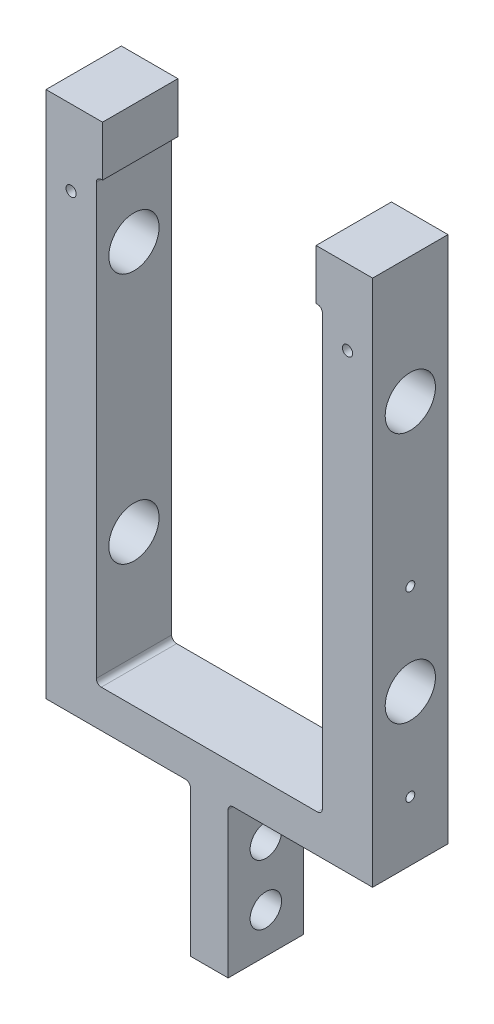
SolidWorks part; units mm, degrees
material "6061 Alloy"
ref_plane "Front Plane" through (0, 0, 0) normal (0, 0, 1) x (1, 0, 0)
ref_plane "Top Plane" through (0, 0, 0) normal (0, 1, 0) x (1, 0, 0)
ref_plane "Right Plane" through (0, 0, 0) normal (1, 0, 0) x (0, 0, -1)
sketch "Sketch1" plane through (0, 0, 0) normal (0, 0, 1) x (1, 0, 0)
  line L7 (9.525, 0) -> (-9.525, 0)
  line L13 (-9.525, 0) -> (-9.525, 19.05)
  line L14 (-9.525, 19.05) -> (-41.275, 19.05)
  line L15 (-41.275, 19.05) -> (-41.275, 131.5967)
  line L17 (-28.575, 139.7) -> (-28.575, 28.575)
  line L18 (-28.575, 28.575) -> (28.575, 28.575)
  line L19 (0, 29.8154) -> (0, -13.1535) construction
  line L20 (28.575, 139.7) -> (28.575, 28.575)
  line L22 (41.275, 19.05) -> (41.275, 131.5967)
  line L23 (9.525, 19.05) -> (41.275, 19.05)
  line L24 (9.525, 0) -> (9.525, 19.05)
  line L25 (41.275, 131.5967) -> (41.275, 152.4)
  line L26 (41.275, 152.4) -> (-41.275, 152.4)
  line L27 (-41.275, 152.4) -> (-41.275, 131.5967)
  line L29 (28.575, 139.7) -> (-28.575, 139.7)
  point P12 (0, 28.575)
  point P17 (0, 0)
  dimension "D1" = 19.05
  dimension "D2" = 57.15
  dimension "D3" = 19.05
  dimension "D4" = 82.55
  dimension "D5" = 111.125
  dimension "D6" = 12.7
  dimension "D7" = 152.4
extrude "Boss-Extrude1" add sketch "Sketch1" along normal mid plane 19.05
sketch "Sketch2" plane through (-41.275, 0, 0) normal (-1, 0, 0) x (0, 0, 1)
  line L0 (-26.0251, 0) -> (40.3307, 0) construction
  line L1 (0, 127) -> (0, 0) construction
  circle A0 centre (0, 57.15) radius 6.35
  circle A1 centre (0, 120.65) radius 6.35
  dimension "D2" = 12.7
  dimension "D1" = 12.7
  dimension "D4" = 63.5
  dimension "D3" = 57.15
extrude "Cut-Extrude1" cut sketch "Sketch2" against normal through all
sketch "Sketch4" plane through (0, 0, -9.525) normal (0, 0, -1) x (-1, 0, 0)
  line L1 (9.525, 0) -> (-9.525, 0) construction
  line L2 (9.525, 0) -> (9.525, 19.05) construction
  line L3 (9.525, 19.05) -> (-9.525, 19.05) construction
  line L4 (-9.525, 0) -> (-9.525, 19.05) construction
  line L5 (-4.7625, 19.0579) -> (4.7625, 19.0579) construction
  line L6 (-4.7625, 19.0579) -> (-4.7625, 0) construction
  line L7 (-4.7625, 0) -> (4.7625, 0) construction
  line L8 (4.7625, 19.0579) -> (4.7625, 0) construction
  line L9 (-4.7625, 19.0579) -> (4.7625, 0) construction
  line L10 (-4.7625, 0) -> (4.7625, 19.0579) construction
  line L11 (-9.525, 19.05) -> (-4.7625, 19.05)
  line L12 (-9.525, 19.05) -> (-9.525, 0)
  line L13 (-9.525, 0) -> (-4.7625, 0)
  line L14 (-4.7625, 19.05) -> (-4.7625, 0)
  line L15 (4.7625, 19.0579) -> (9.525, 19.0579)
  line L16 (4.7625, 19.0579) -> (4.7625, 0)
  line L17 (4.7625, 0) -> (9.525, 0)
  line L18 (9.525, 19.0579) -> (9.525, 0)
  point P6 (0, 9.529)
  dimension "D1" = 9.525
extrude "Cut-Extrude2" cut sketch "Sketch4" against normal through all
sketch "Sketch5" plane through (-4.7625, 0, 0) normal (-1, 0, 0) x (0, 0, 1)
  circle A0 centre (0, 6.35) radius 4.7625
  dimension "D1" = 9.525
  dimension "D2" = 6.35
sketch "Sketch6" plane through (41.275, 0, 0) normal (-1, 0, 0) x (0, 0, 1)
  line L0 (0, 80.1624) -> (0, 34.1376) construction
  point P5 (0, 57.15)
  dimension "D1" = 46.0248
hole_wizard "#4-40 Tapped Hole2" positions "Sketch12" profile "Sketch13" tap size "#4-40" standard "ANSI Inch"
sketch "Sketch12" plane through (41.275, 0, 0) normal (1, 0, 0) x (0, 0, -1)
  point P0 (0, 80.1624)
  point P3 (0, 34.1376)
sketch "Sketch13" plane through (41.275, 80.1624, 0) normal (0, 1, 0) x (0, 0, -1)
  line L0 (0, 0) -> (0, 13.3792)
  line L1 (0, 13.3792) -> (1.1303, 12.7)
  line L2 (1.1303, 12.7) -> (1.1303, 0)
  line L5 (1.1303, 0) -> (0, 0)
  line L10 (0, 13.3792) -> (-1.1303, 12.7) construction
  line L11 (0, -6.35) -> (0, 107.95) construction
  dimension "Tap Drill Dia." = 2.2606
  dimension "Tap Drill Depth" = 12.7
  dimension "Drill Angle" = 118
cosmetic thread "Hole Thread5" parameters "D1"=82.55, "D2"=2.8448
cosmetic thread "Hole Thread6" parameters "D1"=82.55, "D2"=2.8448
sketch "Sketch14" plane through (0, 0, 0) normal (0, -1, 0) x (1, 0, 0)
  line L1 (4.7625, -9.525) -> (-4.7625, -9.525)
  line L2 (4.7625, -9.525) -> (4.7625, 9.525)
  line L3 (4.7625, 9.525) -> (-4.7625, 9.525)
  line L4 (-4.7625, -9.525) -> (-4.7625, 9.525)
extrude "Boss-Extrude2" add sketch "Sketch14" along normal blind 19.05
hole_wizard "Hole1" positions "Sketch15" profile "Sketch16" legacy end condition through all
sketch "Sketch15" plane through (-4.7625, 0, 0) normal (-1, 0, 0) x (0, 0, 1)
  point P0 (0, 6.35)
  point P3 (0, -8.89)
  dimension "D1" = 8.89
sketch "Sketch16" plane through (-4.7625, 6.35, 0) normal (0, 1, 0) x (0, 0, 1)
  line L0 (0, 0) -> (0, 48.4245)
  line L1 (0, 48.4245) -> (3.9726, 46.0375)
  line L2 (3.9726, 46.0375) -> (3.9726, 0)
  line L4 (3.9726, 0) -> (0, 0)
  line L6 (0, 48.4245) -> (-3.9726, 46.0375) construction
  line L7 (0, -4.2442) -> (0, 117.3081) construction
  dimension "Diameter" = 7.9451
  dimension "Depth" = 46.0375
  dimension "Drill Angle" = 118
fillet "Fillet1" radius 1.27 6 edges at (4.7625, 19.05, 0) (-4.7625, 19.0579, 0) (-28.575, 28.575, 0) (28.575, 28.575, 0) (28.575, 139.7, 0) (-28.575, 139.7, 0)
sketch "Sketch17" plane through (0, 0, 9.525) normal (0, 0, 1) x (1, 0, 0)
  line L0 (0, 152.4) -> (0, 117.2896) construction
  line L1 (41.275, 152.4) -> (-41.275, 152.4) construction
  line L2 (23.5336, 152.4) -> (23.5336, 139.7) construction
  line L3 (27.305, 139.7) -> (-27.305, 139.7) construction
  line L4 (23.5336, 146.05) -> (-38.274, 146.05) construction
  line L6 (-26.9875, 152.4) -> (26.9875, 152.4)
  line L7 (-26.9875, 152.4) -> (-26.9875, 139.7)
  line L8 (-26.9875, 139.7) -> (26.9875, 139.7)
  line L9 (26.9875, 152.4) -> (26.9875, 139.7)
  line L10 (-26.9875, 152.4) -> (26.9875, 139.7) construction
  line L11 (-26.9875, 139.7) -> (26.9875, 152.4) construction
  point P11 (0, 146.05)
  point P12 (0, 146.05)
  dimension "D1" = 53.975
extrude "Cut-Extrude3" cut sketch "Sketch17" against normal through all
hole_wizard "#5-40 Tapped Hole1" positions "Sketch18" profile "Sketch19" tap size "#5-40" standard "ANSI Inch" end condition through all
sketch "Sketch18" plane through (0, 0, 9.525) normal (0, 0, 1) x (1, 0, 0)
  line L4 (-41.275, 133.35) -> (-28.575, 133.35) construction
  line L5 (-41.275, 152.4) -> (-41.275, 19.05) construction
  line L6 (-28.575, 138.43) -> (-28.575, 29.845) construction
  line L7 (-26.9875, 152.4) -> (-41.275, 152.4) construction
  line L8 (28.575, 133.35) -> (41.275, 133.35) construction
  line L9 (28.575, 29.845) -> (28.575, 138.43) construction
  line L10 (41.275, 19.05) -> (41.275, 152.4) construction
  point P18 (-34.925, 133.35)
  point P31 (34.925, 133.35)
  point P34 (34.925, 133.35)
  dimension "D1" = 19.05
sketch "Sketch19" plane through (34.925, 133.35, 9.525) normal (1, 0, 0) x (0, -1, 0)
  line L0 (0, 0) -> (0, 19.05)
  line L1 (0, 19.05) -> (1.289, 19.05)
  line L2 (1.289, 19.05) -> (1.289, 0)
  line L5 (1.289, 0) -> (0, 0)
  line L11 (0, -6.35) -> (0, 107.95) construction
  dimension "Thru Tap Drill Dia." = 2.5781
  dimension "Thru Tap Drill Depth" = 19.05
cosmetic thread "Hole Thread7" parameters "D2"=3.175
cosmetic thread "Hole Thread8" parameters "D2"=3.175
equation "\"BoomDistance\"=2.5"
equation "\"D4@Sketch2\"=\"BoomDistance\""
